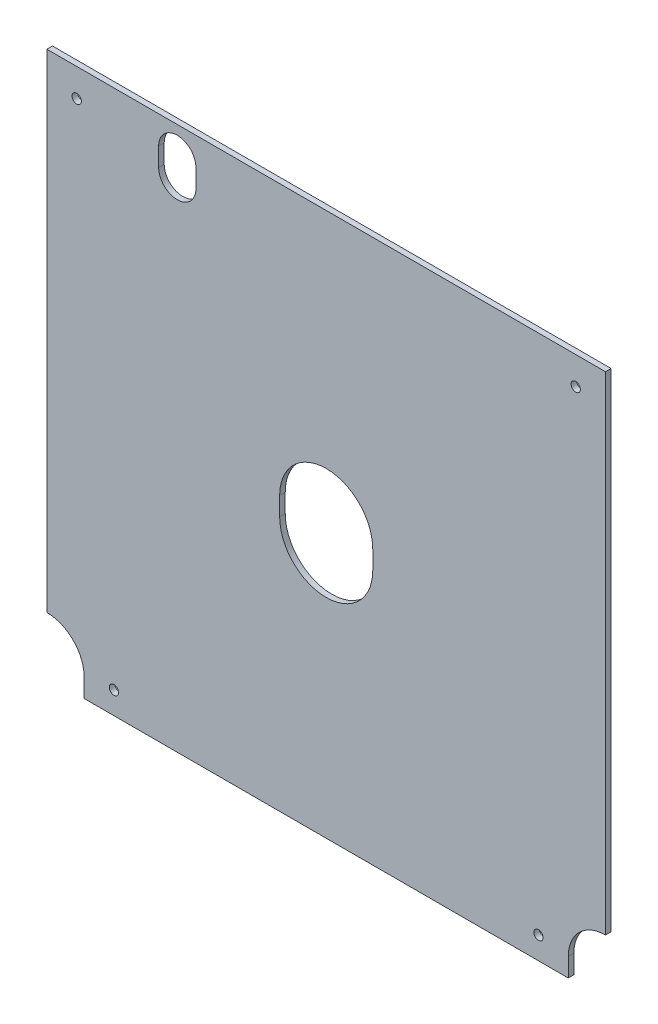
SolidWorks part; units mm, degrees
ref_plane "Face" through (0, 0, 0) normal (0, 0, 1) x (1, 0, 0)
ref_plane "Dessus" through (0, 0, 0) normal (0, 1, 0) x (1, 0, 0)
ref_plane "Droite" through (0, 0, 0) normal (1, 0, 0) x (0, 0, -1)
sketch "Esquisse1" plane through (0, 0, 0) normal (0, 0, 1) x (1, 0, 0)
  line L0 (0, 0) -> (0, 292) construction
  line L1 (150, 292) -> (-150, 292)
  line L2 (-150, 292) -> (-150, 30)
  line L3 (130, 0) -> (-130, 0)
  line L4 (-130, 0) -> (-130, 10)
  line L5 (-150, 30) -> (-150, 0) construction
  line L6 (150, 30) -> (150, 0) construction
  line L7 (130, 0) -> (130, 10)
  line L8 (150, 292) -> (150, 30)
  line L9 (-25, 137) -> (-25, 147)
  line L10 (25, 147) -> (25, 137)
  line L11 (-90, 267) -> (-90, 277)
  line L12 (-70, 277) -> (-70, 267)
  arc A0 (-150, 30) -> (-130, 10) centre (-150, 10) cw
  arc A1 (150, 30) -> (130, 10) centre (150, 10) ccw
  arc A2 (-25, 147) -> (25, 147) centre (0, 147) cw
  arc A3 (-25, 137) -> (25, 137) centre (0, 137) ccw
  arc A4 (-90, 277) -> (-70, 277) centre (-80, 277) cw
  arc A5 (-90, 267) -> (-70, 267) centre (-80, 267) ccw
  circle A6 centre (134, 277) radius 2.5
  circle A7 centre (-134, 277) radius 2.5
  circle A8 centre (114, 12) radius 2.5
  circle A9 centre (-114, 12) radius 2.5
  dimension "D3" = 20
  dimension "D7" = 15
  dimension "D13" = 16
  dimension "D14" = 5
  dimension "D15" = 12
  dimension "D16" = 16
  dimension "D1" = 292
  dimension "D2" = 150
  dimension "D4" = 30
  dimension "D5" = 50
  dimension "D6" = 10
  dimension "D8" = 145
  dimension "D9" = 20
  dimension "D10" = 10
  dimension "D11" = 15
  dimension "D12" = 70
extrude "Extrusion1" add sketch "Esquisse1" along normal blind 3
